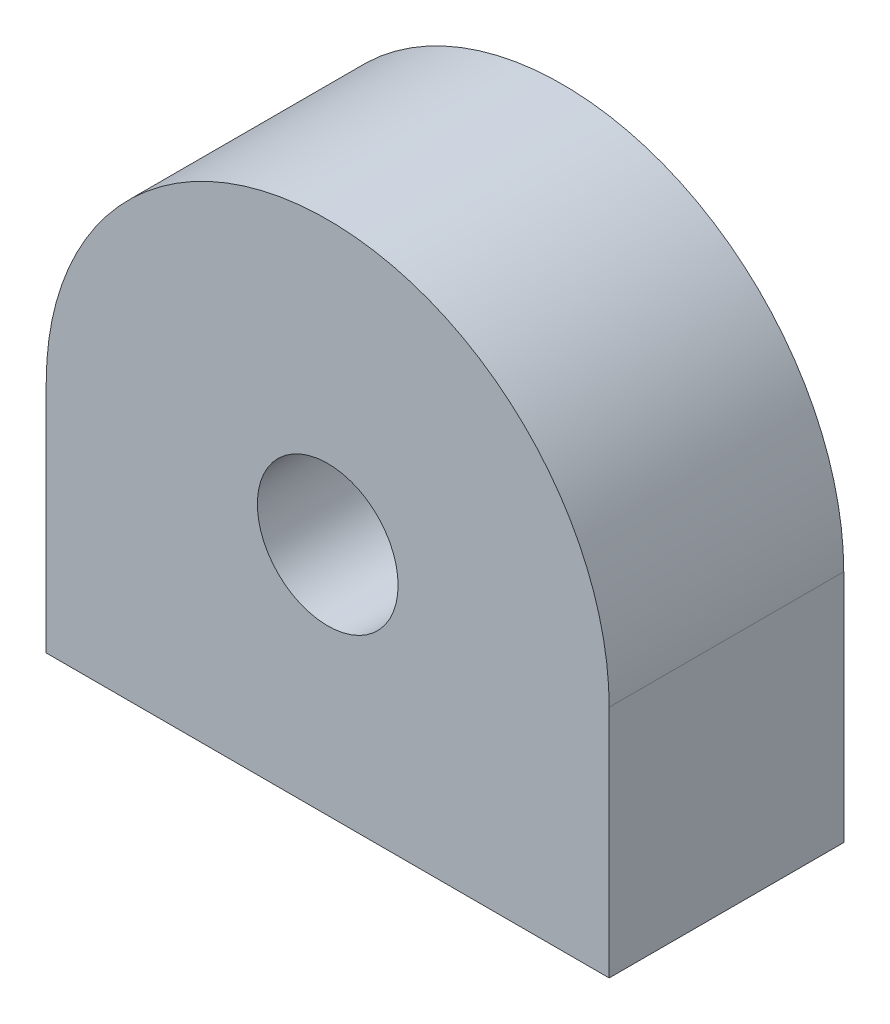
SolidWorks part; units mm, degrees
ref_plane "Front Plane" through (0, 0, 0) normal (0, 0, 1) x (1, 0, 0)
ref_plane "Top Plane" through (0, 0, 0) normal (0, 1, 0) x (1, 0, 0)
ref_plane "Right Plane" through (0, 0, 0) normal (1, 0, 0) x (0, 0, -1)
sketch "Sketch2" plane through (0, 0, 0) normal (0, 0, 1) x (1, 0, 0)
  line L2 (-6, 0) -> (-6, -5)
  line L3 (-6, -5) -> (6, -5)
  line L4 (6, 0) -> (6, -5)
  arc A0 (-6, 0) -> (6, 0) centre (0, 0) cw
  dimension "D2" = 6
  dimension "D1" = 5
extrude "Boss-Extrude1" add sketch "Sketch2" along normal mid plane 5 contours A0 L4 L3 L2
sketch "Sketch4" plane through (0, 0, 0) normal (0, 0, 1) x (1, 0, 0)
  circle A0 centre (0, 0) radius 1.5
  dimension "D1" = 3
extrude "Cut-Extrude1" cut sketch "Sketch4" against normal through all and the other way through all
equation "\"height\"= 5mm"
equation "\"width\"= 5mm"
equation "\"thick\"= 5mm"
equation "\"outer radi\"= 6mm"
equation "\"inner radi\"= 3mm"
equation "\"D1@Sketch2\"=\"height\""
equation "\"D2@Sketch2\"=\"outer radi\""
equation "\"D1@Boss-Extrude1\"=\"thick\""
equation "\"D1@Sketch4\"=\"inner radi\""
